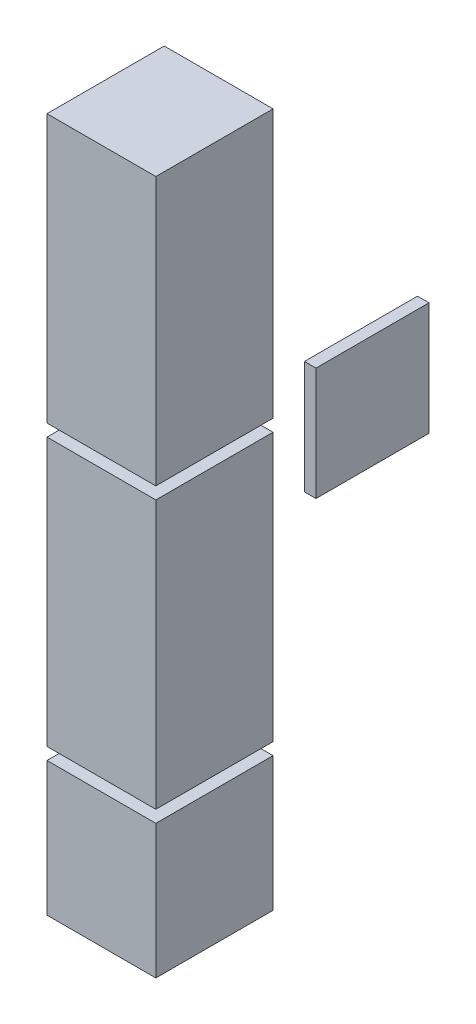
SolidWorks part; units mm, degrees
ref_plane "Front Plane" through (0, 0, 0) normal (0, 0, 1) x (1, 0, 0)
ref_plane "Top Plane" through (0, 0, 0) normal (0, 1, 0) x (1, 0, 0)
ref_plane "Right Plane" through (0, 0, 0) normal (1, 0, 0) x (0, 0, -1)
ref_plane "top-of-PCB" through (1.5875, 0, 0) normal (1, 0, 0) x (0, 0, -1)
sketch "Sketch2" plane through (1.5875, 0, 0) normal (1, 0, 0) x (0, 0, -1)
  line L1 (-5, 215) -> (23, 215)
  line L2 (-5, 215) -> (-5, 151)
  line L3 (-5, 151) -> (23, 151)
  line L4 (23, 215) -> (23, 151)
  line L5 (-5, 148.1) -> (23, 148.1)
  line L6 (-5, 148.1) -> (-5, 84.1)
  line L7 (-5, 84.1) -> (23, 84.1)
  line L8 (23, 148.1) -> (23, 84.1)
  line L9 (-5, 81.2) -> (23, 81.2) construction
  line L10 (-5, 81.2) -> (-5, 17.2) construction
  line L11 (-5, 17.2) -> (23, 17.2) construction
  line L12 (23, 81.2) -> (23, 17.2) construction
  line L14 (-5, 81.2) -> (23, 81.2)
  line L15 (-5, 81.2) -> (-5, 49.2)
  line L16 (-5, 49.2) -> (23, 49.2)
  line L17 (23, 81.2) -> (23, 49.2)
  dimension "D1" = 3
extrude "Boss-Extrude2" add sketch "Sketch2" along normal blind 26 separate body
sketch "Sketch3" plane through (1.5875, 0, 0) normal (1, 0, 0) x (0, 0, -1)
  line L1 (56.5, 133) -> (83.5, 133)
  line L2 (56.5, 133) -> (56.5, 106)
  line L3 (56.5, 106) -> (83.5, 106)
  line L4 (83.5, 133) -> (83.5, 106)
extrude "Boss-Extrude3" add sketch "Sketch3" along normal blind 2.75 separate body
